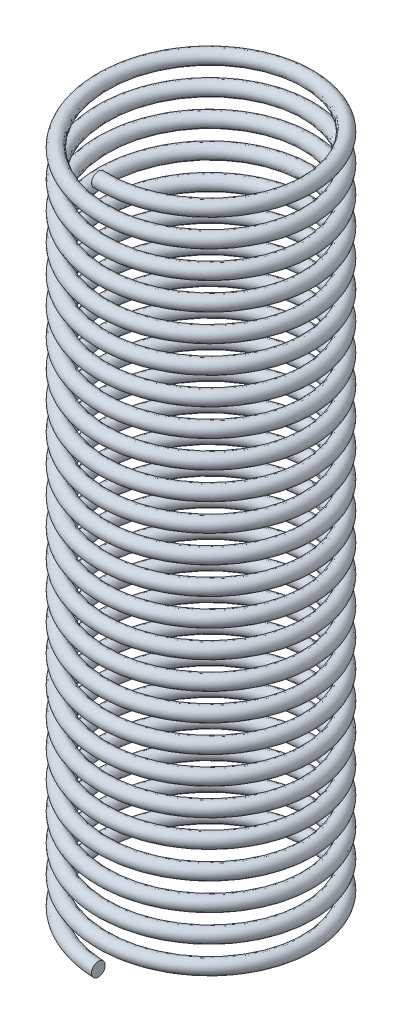
SolidWorks part; units mm, degrees
ref_plane "Front Plane" through (0, 0, 0) normal (0, 0, 1) x (1, 0, 0)
ref_plane "Top Plane" through (0, 0, 0) normal (0, 1, 0) x (1, 0, 0)
ref_plane "Right Plane" through (0, 0, 0) normal (1, 0, 0) x (0, 0, -1)
sketch "Sketch1" plane through (0, 0, 0) normal (0, 1, 0) x (1, 0, 0)
  circle A0 centre (0, 0) radius 75
  dimension "D1" = 150
curve "Helix/Spiral1" pitch 20 height 500 turns 25
sketch "Sketch2" plane through (0, 0, 0) normal (1, 0, 0) x (0, 0, -1)
  circle A0 centre (-75, 0) radius 5
  spline S0 degree 3 poles (-75, 0) (-75, 0.1732) (-74.3306, 0.5204) (-71.3449, 1.0406) (-66.4574, 1.5609) (-59.7983, 2.0812) (-51.545, 2.6015) (-41.9177, 3.1217) (-31.1729, 3.642) (-19.5972, 4.1623) (-7.499, 4.6826) (4.7991, 5.2029) (16.9693, 5.7232) (28.6871, 6.2435) (39.6401, 6.7638) (49.5365, 7.2841) (58.1123, 7.8044) (65.1389, 8.3247) (70.4291, 8.845) (73.8418, 9.3652) (75.286, 9.8855) (74.7233, 10.4058) (72.1686, 10.9261) (67.69, 11.4464) (61.4069, 11.9667) (53.4869, 12.487) (44.141, 13.0073) (33.6185, 13.5276) (22.1997, 14.0479) (10.1891, 14.5682) (-2.0931, 15.0884) (-14.3195, 15.6087) (-26.1641, 16.129) (-37.3113, 16.6493) (-47.4639, 17.1696) (-56.3511, 17.6899) (-63.7362, 18.2102) (-69.4222, 18.7305) (-73.2575, 19.2508) (-75.14, 19.7711) (-75.0193, 20.2914) (-72.8988, 20.8117) (-68.835, 21.3319) (-62.9362, 21.8522) (-55.3597, 22.3725) (-46.3073, 22.8928) (-36.0205, 23.4131) (-24.7735, 23.9334) (-12.8661, 24.4537) (-0.6157, 24.974) (11.6511, 25.4943) (23.6074, 26.0146) (34.9343, 26.5349) (45.3299, 27.0552) (54.5171, 27.5754) (62.2511, 28.0957) (68.3255, 28.616) (72.5785, 29.1363) (74.8968, 29.6566) (75.2184, 30.1769) (73.5349, 30.6972) (69.8911, 31.2175) (64.3841, 31.7378) (57.1608, 32.2581) (48.4137, 32.7784) (38.376, 33.2986) (27.3153, 33.8189) (15.5264, 34.3392) (3.3236, 34.8595) (-8.9677, 35.3798) (-21.0201, 35.9001) (-32.5121, 36.4204) (-43.1373, 36.9407) (-52.6127, 37.461) (-60.6854, 37.9813) (-67.1405, 38.5016) (-71.8057, 39.0219) (-74.5567, 39.5421) (-75.3202, 40.0624) (-74.0758, 40.5827) (-70.8568, 41.103) (-65.7488, 41.6233) (-58.8881, 42.1436) (-50.4575, 42.6639) (-40.6819, 43.1842) (-29.8218, 43.7045) (-18.1667, 44.2248) (-6.0273, 44.7451) (6.2728, 45.2653) (18.4056, 45.7856) (30.0478, 46.3059) (40.889, 46.8262) (50.6402, 47.3465) (59.0414, 47.8668) (65.8686, 48.3871) (70.94, 48.9074) (74.1203, 49.4277) (75.3246, 49.948) (74.521, 50.4683) (71.7308, 50.9886) (67.0284, 51.5088) (60.5392, 52.0291) (52.4361, 52.5494) (42.9352, 53.0697) (32.2897, 53.59) (20.7835, 54.1103) (8.7232, 54.6306) (-3.5697, 55.1509) (-15.7673, 55.6712) (-27.5447, 56.1915) (-38.5878, 56.7118) (-48.6022, 57.232) (-57.3209, 57.7523) (-64.5117, 58.2726) (-69.9826, 58.7929) (-73.588, 59.3132) (-75.2317, 59.8335) (-74.8698, 60.3538) (-72.5121, 60.8741) (-68.2214, 61.3944) (-62.112, 61.9147) (-54.3469, 62.435) (-45.133, 62.9553) (-34.7159, 63.4755) (-23.3734, 63.9958) (-11.4078, 64.5161) (0.8619, 65.0364) (13.1087, 65.5567) (25.006, 66.077) (36.2366, 66.5973) (46.5013, 67.1176) (55.5264, 67.6379) (63.0712, 68.1582) (68.9347, 68.6785) (72.9606, 69.1988) (75.0414, 69.719) (75.1219, 70.2393) (73.1997, 70.7596) (69.3262, 71.2799) (63.6046, 71.8002) (56.1874, 72.3205) (47.2724, 72.8408) (37.0972, 73.3611) (25.9331, 73.8814) (14.0776, 74.4017) (1.8469, 74.922) (-10.4331, 75.4422) (-22.4349, 75.9625) (-33.8387, 76.4828) (-44.3404, 77.0031) (-53.6601, 77.5234) (-61.5493, 78.0437) (-67.7977, 78.564) (-72.2388, 79.0843) (-74.7542, 79.6046) (-75.2768, 80.1249) (-73.7926, 80.6452) (-70.3413, 81.1655) (-65.0149, 81.6857) (-57.9552, 82.206) (-49.3507, 82.7263) (-39.4305, 83.2466) (-28.4592, 83.7669) (-16.7292, 84.2872) (-4.5533, 84.8075) (7.744, 85.3278) (19.8349, 85.8481) (31.397, 86.3684) (42.1221, 86.8887) (51.7243, 87.4089) (59.9477, 87.9292) (66.573, 88.4495) (71.4237, 88.9698) (74.3703, 89.4901) (75.3343, 90.0104) (74.2901, 90.5307) (71.2655, 91.051) (66.3411, 91.5713) (59.6482, 92.0916) (51.3651, 92.6119) (41.7128, 93.1322) (30.9486, 93.6524) (19.3593, 94.1727) (7.2539, 94.693) (-5.0449, 95.2133) (-17.2091, 95.7336) (-28.9146, 96.2539) (-39.8494, 96.7742) (-49.7218, 97.2945) (-58.2687, 97.8148) (-65.2623, 98.3351) (-70.5161, 98.8554) (-73.8902, 99.3757) (-75.2945, 99.8959) (-74.6916, 100.4162) (-72.0975, 100.9365) (-67.5815, 101.4568) (-61.2639, 101.9771) (-53.3132, 102.4974) (-43.9412, 103.0177) (-33.3979, 103.538) (-21.9642, 104.0583) (-9.9451, 104.5786) (2.3392, 105.0989) (14.5612, 105.6191) (26.3949, 106.1394) (37.5251, 106.6597) (47.6549, 107.18) (56.5143, 107.7003) (63.8671, 108.2206) (69.5174, 108.7409) (73.3146, 109.2612) (75.1573, 109.7815) (74.9964, 110.3018) (72.8363, 110.8221) (68.7346, 111.3424) (62.8005, 111.8626) (55.1923, 112.3829) (46.1128, 112.9032) (35.8041, 113.4235) (24.5408, 113.9438) (12.6234, 114.4641) (0.3694, 114.9844) (-11.8944, 115.5047) (-23.8411, 116.025) (-35.1523, 116.5453) (-45.5264, 117.0656) (-54.6868, 117.5858) (-62.3894, 118.1061) (-68.4289, 118.6264) (-72.6441, 119.1467) (-74.9229, 119.667) (-75.2043, 120.1873) (-73.481, 120.7076) (-69.7988, 121.2279) (-64.2559, 121.7482) (-57.0001, 122.2685) (-48.2248, 122.7888) (-38.1639, 123.3091) (-27.0857, 123.8293) (-15.2854, 124.3496) (-3.0776, 124.8699) (9.2122, 125.3902) (21.2565, 125.9105) (32.734, 126.4308) (43.339, 126.9511) (52.7886, 127.4714) (60.831, 127.9917) (67.2518, 128.512) (71.8798, 129.0323) (74.5916, 129.5525) (75.315, 130.0728) (74.0306, 130.5931) (70.7727, 131.1134) (65.6282, 131.6337) (58.7342, 132.154) (50.2744, 132.6743) (40.4744, 133.1946) (29.5955, 133.7149) (17.9276, 134.2352) (5.7818, 134.7555) (-6.5181, 135.2758) (-18.6443, 135.796) (-30.2735, 136.3163) (-41.0956, 136.8366) (-50.8222, 137.3569) (-59.194, 137.8772) (-65.9878, 138.3975) (-71.0225, 138.9178) (-74.1639, 139.4381) (-75.3283, 139.9584) (-74.4845, 140.4787) (-71.6552, 140.999) (-66.9156, 141.5193) (-60.3923, 142.0395) (-52.259, 142.5598) (-42.7326, 143.0801) (-32.067, 143.6004) (-20.5466, 144.1207) (-8.4785, 144.641) (3.8156, 145.1613) (16.0081, 145.6816) (27.7738, 146.2019) (38.7991, 146.7222) (48.7901, 147.2425) (57.4804, 147.7627) (64.6385, 148.283) (70.0734, 148.8033) (73.6403, 149.3236) (75.2442, 149.8439) (74.8421, 150.3642) (72.445, 150.8845) (68.1166, 151.4048) (61.9723, 151.9251) (54.176, 152.4454) (44.9355, 152.9657) (34.4971, 153.486) (23.1391, 154.0062) (11.1643, 154.5265) (-1.1082, 155.0468) (-13.3511, 155.5671) (-25.2381, 156.0874) (-36.4524, 156.6077) (-46.6948, 157.128) (-55.6925, 157.6483) (-63.2056, 158.1686) (-69.0337, 158.6889) (-73.0215, 159.2092) (-75.0628, 159.7294) (-75.103, 160.2497) (-73.1411, 160.77) (-69.2294, 161.2903) (-63.4722, 161.8106) (-56.023, 162.3309) (-47.0804, 162.8512) (-36.8826, 163.3715) (-25.7017, 163.8918) (-13.8356, 164.4121) (-1.6007, 164.9324) (10.6769, 165.4527) (22.6699, 165.9729) (34.0585, 166.4932) (44.5392, 167.0135) (53.8326, 167.5338) (61.691, 168.0541) (67.9047, 168.5744) (72.3083, 169.0947) (74.7843, 169.615) (75.2667, 170.1353) (73.7426, 170.6556) (70.2528, 171.1759) (64.8901, 171.6961) (57.7976, 172.2164) (49.1643, 172.7367) (39.2204, 173.257) (28.231, 173.7773) (16.489, 174.2976) (4.3075, 174.8179) (-7.9889, 175.3382) (-20.0723, 175.8585) (-31.6207, 176.3788) (-42.3261, 176.8991) (-51.9031, 177.4194) (-60.0966, 177.9396) (-66.688, 178.4599) (-71.5016, 178.9802) (-74.4091, 179.5005) (-75.3331, 180.0208) (-74.2488, 180.5411) (-71.1853, 181.0614) (-66.224, 181.5817) (-59.4974, 182.102) (-51.1847, 182.6223) (-41.5075, 183.1426) (-30.7239, 183.6629) (-19.1211, 184.1831) (-7.0087, 184.7034) (5.2906, 185.2237) (17.4488, 185.744) (29.1419, 186.2643) (40.0581, 186.7846) (49.9065, 187.3049) (58.4245, 187.8252) (65.385, 188.3455) (70.6024, 188.8658) (73.9378, 189.3861) (75.3021, 189.9063) (74.659, 190.4266) (72.0257, 190.9469) (67.4723, 191.4672) (61.1203, 191.9875) (53.1389, 192.5078) (43.741, 193.0281) (33.177, 193.5484) (21.7285, 194.0687) (9.7009, 194.589) (-2.5854, 195.1093) (-14.8027, 195.6296) (-26.6255, 196.1498) (-37.7384, 196.6701) (-47.8454, 197.1904) (-56.6768, 197.7107) (-63.9974, 198.231) (-69.612, 198.7513) (-73.3708, 199.2716) (-75.1737, 199.7919) (-74.9727, 200.3122) (-72.7731, 200.8325) (-68.6334, 201.3528) (-62.6642, 201.873) (-55.0244, 202.3933) (-45.9178, 202.9136) (-35.5872, 203.4339) (-24.3078, 203.9542) (-12.3805, 204.4745) (-0.1231, 204.9948) (12.1375, 205.5151) (24.0746, 206.0354) (35.3699, 206.5557) (45.7223, 207.076) (54.8559, 207.5963) (62.5271, 208.1165) (68.5315, 208.6368) (72.709, 209.1571) (74.9482, 209.6774) (75.1894, 210.1977) (73.4263, 210.718) (69.7058, 211.2383) (64.127, 211.7586) (56.8388, 212.2789) (48.0353, 212.7992) (37.9514, 213.3195) (26.8557, 213.8398) (15.0441, 214.36) (2.8315, 214.8803) (-9.4566, 215.4006) (-21.4926, 215.9209) (-32.9557, 216.4412) (-43.5402, 216.9615) (-52.9641, 217.4818) (-60.976, 218.0021) (-67.3624, 218.5224) (-71.9531, 219.0427) (-74.6257, 219.563) (-75.3089, 220.0832) (-73.9846, 220.6035) (-70.688, 221.1238) (-65.5069, 221.6441) (-58.5796, 222.1644) (-50.0907, 222.6847) (-40.2665, 223.205) (-29.3689, 223.7253) (-17.6883, 224.2456) (-5.5362, 224.7659) (6.7635, 225.2862) (18.8828, 225.8065) (30.4988, 226.3267) (41.3018, 226.847) (51.0037, 227.3673) (59.346, 227.8876) (66.1063, 228.4079) (71.1043, 228.9282) (74.2068, 229.4485) (75.3311, 229.9688) (74.4472, 230.4891) (71.5788, 231.0094) (66.8022, 231.5297) (60.2448, 232.0499) (52.0813, 232.5702) (42.5296, 233.0905) (31.844, 233.6108) (20.3096, 234.1311) (8.2338, 234.6514) (-4.0616, 235.1717) (-16.2486, 235.692) (-28.0025, 236.2123) (-39.01, 236.7326) (-48.9775, 237.2529) (-57.6393, 237.7732) (-64.7646, 238.2934) (-70.1635, 238.8137) (-73.6919, 239.334) (-75.2558, 239.8543) (-74.8136, 240.3746) (-72.377, 240.8949) (-68.011, 241.4152) (-61.832, 241.9355) (-54.0046, 242.4558) (-44.7376, 242.9761) (-34.278, 243.4964) (-22.9046, 244.0166) (-10.9207, 244.5369) (1.3544, 245.0572) (13.5934, 245.5775) (25.4701, 246.0978) (36.6677, 246.6181) (46.8879, 247.1384) (55.8581, 247.6587) (63.3393, 248.179) (69.1319, 248.6993) (73.0817, 249.2196) (75.0833, 249.7399) (75.0833, 250.2601) (73.0817, 250.7804) (69.1319, 251.3007) (63.3393, 251.821) (55.8581, 252.3413) (46.8879, 252.8616) (36.6677, 253.3819) (25.4701, 253.9022) (13.5934, 254.4225) (1.3544, 254.9428) (-10.9207, 255.4631) (-22.9046, 255.9834) (-34.278, 256.5036) (-44.7376, 257.0239) (-54.0046, 257.5442) (-61.832, 258.0645) (-68.011, 258.5848) (-72.377, 259.1051) (-74.8136, 259.6254) (-75.2558, 260.1457) (-73.6919, 260.666) (-70.1635, 261.1863) (-64.7646, 261.7066) (-57.6393, 262.2268) (-48.9775, 262.7471) (-39.01, 263.2674) (-28.0025, 263.7877) (-16.2486, 264.308) (-4.0616, 264.8283) (8.2338, 265.3486) (20.3096, 265.8689) (31.844, 266.3892) (42.5296, 266.9095) (52.0813, 267.4298) (60.2448, 267.9501) (66.8022, 268.4703) (71.5788, 268.9906) (74.4472, 269.5109) (75.3311, 270.0312) (74.2068, 270.5515) (71.1043, 271.0718) (66.1063, 271.5921) (59.346, 272.1124) (51.0037, 272.6327) (41.3018, 273.153) (30.4988, 273.6733) (18.8828, 274.1935) (6.7635, 274.7138) (-5.5362, 275.2341) (-17.6883, 275.7544) (-29.3689, 276.2747) (-40.2665, 276.795) (-50.0907, 277.3153) (-58.5796, 277.8356) (-65.5069, 278.3559) (-70.688, 278.8762) (-73.9846, 279.3965) (-75.3089, 279.9168) (-74.6257, 280.437) (-71.9531, 280.9573) (-67.3624, 281.4776) (-60.976, 281.9979) (-52.9641, 282.5182) (-43.5402, 283.0385) (-32.9557, 283.5588) (-21.4926, 284.0791) (-9.4566, 284.5994) (2.8315, 285.1197) (15.0441, 285.64) (26.8557, 286.1602) (37.9514, 286.6805) (48.0353, 287.2008) (56.8388, 287.7211) (64.127, 288.2414) (69.7058, 288.7617) (73.4263, 289.282) (75.1894, 289.8023) (74.9482, 290.3226) (72.709, 290.8429) (68.5315, 291.3632) (62.5271, 291.8835) (54.8559, 292.4037) (45.7223, 292.924) (35.3699, 293.4443) (24.0746, 293.9646) (12.1375, 294.4849) (-0.1231, 295.0052) (-12.3805, 295.5255) (-24.3078, 296.0458) (-35.5872, 296.5661) (-45.9178, 297.0864) (-55.0244, 297.6067) (-62.6642, 298.127) (-68.6334, 298.6472) (-72.7731, 299.1675) (-74.9727, 299.6878) (-75.1737, 300.2081) (-73.3708, 300.7284) (-69.612, 301.2487) (-63.9974, 301.769) (-56.6768, 302.2893) (-47.8454, 302.8096) (-37.7384, 303.3299) (-26.6255, 303.8502) (-14.8027, 304.3704) (-2.5854, 304.8907) (9.7009, 305.411) (21.7285, 305.9313) (33.177, 306.4516) (43.741, 306.9719) (53.1389, 307.4922) (61.1203, 308.0125) (67.4723, 308.5328) (72.0257, 309.0531) (74.659, 309.5734) (75.3021, 310.0937) (73.9378, 310.6139) (70.6024, 311.1342) (65.385, 311.6545) (58.4245, 312.1748) (49.9065, 312.6951) (40.0581, 313.2154) (29.1419, 313.7357) (17.4488, 314.256) (5.2906, 314.7763) (-7.0087, 315.2966) (-19.1211, 315.8169) (-30.7239, 316.3371) (-41.5075, 316.8574) (-51.1847, 317.3777) (-59.4974, 317.898) (-66.224, 318.4183) (-71.1853, 318.9386) (-74.2488, 319.4589) (-75.3331, 319.9792) (-74.4091, 320.4995) (-71.5016, 321.0198) (-66.688, 321.5401) (-60.0966, 322.0604) (-51.9031, 322.5806) (-42.3261, 323.1009) (-31.6207, 323.6212) (-20.0723, 324.1415) (-7.9889, 324.6618) (4.3075, 325.1821) (16.489, 325.7024) (28.231, 326.2227) (39.2204, 326.743) (49.1643, 327.2633) (57.7976, 327.7836) (64.8901, 328.3039) (70.2528, 328.8241) (73.7426, 329.3444) (75.2667, 329.8647) (74.7843, 330.385) (72.3083, 330.9053) (67.9047, 331.4256) (61.691, 331.9459) (53.8326, 332.4662) (44.5392, 332.9865) (34.0585, 333.5068) (22.6699, 334.0271) (10.6769, 334.5473) (-1.6007, 335.0676) (-13.8356, 335.5879) (-25.7017, 336.1082) (-36.8826, 336.6285) (-47.0804, 337.1488) (-56.023, 337.6691) (-63.4722, 338.1894) (-69.2294, 338.7097) (-73.1411, 339.23) (-75.103, 339.7503) (-75.0628, 340.2706) (-73.0215, 340.7908) (-69.0337, 341.3111) (-63.2056, 341.8314) (-55.6925, 342.3517) (-46.6948, 342.872) (-36.4524, 343.3923) (-25.2381, 343.9126) (-13.3511, 344.4329) (-1.1082, 344.9532) (11.1643, 345.4735) (23.1391, 345.9938) (34.4971, 346.514) (44.9355, 347.0343) (54.176, 347.5546) (61.9723, 348.0749) (68.1166, 348.5952) (72.445, 349.1155) (74.8421, 349.6358) (75.2442, 350.1561) (73.6403, 350.6764) (70.0734, 351.1967) (64.6385, 351.717) (57.4804, 352.2373) (48.7901, 352.7575) (38.7991, 353.2778) (27.7738, 353.7981) (16.0081, 354.3184) (3.8156, 354.8387) (-8.4785, 355.359) (-20.5466, 355.8793) (-32.067, 356.3996) (-42.7326, 356.9199) (-52.259, 357.4402) (-60.3923, 357.9605) (-66.9156, 358.4807) (-71.6552, 359.001) (-74.4845, 359.5213) (-75.3283, 360.0416) (-74.1639, 360.5619) (-71.0225, 361.0822) (-65.9878, 361.6025) (-59.194, 362.1228) (-50.8222, 362.6431) (-41.0956, 363.1634) (-30.2735, 363.6837) (-18.6443, 364.204) (-6.5181, 364.7242) (5.7818, 365.2445) (17.9276, 365.7648) (29.5955, 366.2851) (40.4744, 366.8054) (50.2744, 367.3257) (58.7342, 367.846) (65.6282, 368.3663) (70.7727, 368.8866) (74.0306, 369.4069) (75.315, 369.9272) (74.5916, 370.4475) (71.8798, 370.9677) (67.2518, 371.488) (60.831, 372.0083) (52.7886, 372.5286) (43.339, 373.0489) (32.734, 373.5692) (21.2565, 374.0895) (9.2122, 374.6098) (-3.0776, 375.1301) (-15.2854, 375.6504) (-27.0857, 376.1707) (-38.1639, 376.6909) (-48.2248, 377.2112) (-57.0001, 377.7315) (-64.2559, 378.2518) (-69.7988, 378.7721) (-73.481, 379.2924) (-75.2043, 379.8127) (-74.9229, 380.333) (-72.6441, 380.8533) (-68.4289, 381.3736) (-62.3894, 381.8939) (-54.6868, 382.4142) (-45.5264, 382.9344) (-35.1523, 383.4547) (-23.8411, 383.975) (-11.8944, 384.4953) (0.3694, 385.0156) (12.6234, 385.5359) (24.5408, 386.0562) (35.8041, 386.5765) (46.1128, 387.0968) (55.1923, 387.6171) (62.8005, 388.1374) (68.7346, 388.6576) (72.8363, 389.1779) (74.9964, 389.6982) (75.1573, 390.2185) (73.3146, 390.7388) (69.5174, 391.2591) (63.8671, 391.7794) (56.5143, 392.2997) (47.6549, 392.82) (37.5251, 393.3403) (26.3949, 393.8606) (14.5612, 394.3809) (2.3392, 394.9011) (-9.9451, 395.4214) (-21.9642, 395.9417) (-33.3979, 396.462) (-43.9412, 396.9823) (-53.3132, 397.5026) (-61.2639, 398.0229) (-67.5815, 398.5432) (-72.0975, 399.0635) (-74.6916, 399.5838) (-75.2945, 400.1041) (-73.8902, 400.6243) (-70.5161, 401.1446) (-65.2623, 401.6649) (-58.2687, 402.1852) (-49.7218, 402.7055) (-39.8494, 403.2258) (-28.9146, 403.7461) (-17.2091, 404.2664) (-5.0449, 404.7867) (7.2539, 405.307) (19.3593, 405.8273) (30.9486, 406.3476) (41.7128, 406.8678) (51.3651, 407.3881) (59.6482, 407.9084) (66.3411, 408.4287) (71.2655, 408.949) (74.2901, 409.4693) (75.3343, 409.9896) (74.3703, 410.5099) (71.4237, 411.0302) (66.573, 411.5505) (59.9477, 412.0708) (51.7243, 412.5911) (42.1221, 413.1113) (31.397, 413.6316) (19.8349, 414.1519) (7.744, 414.6722) (-4.5533, 415.1925) (-16.7292, 415.7128) (-28.4592, 416.2331) (-39.4305, 416.7534) (-49.3507, 417.2737) (-57.9552, 417.794) (-65.0149, 418.3143) (-70.3413, 418.8345) (-73.7926, 419.3548) (-75.2768, 419.8751) (-74.7542, 420.3954) (-72.2388, 420.9157) (-67.7977, 421.436) (-61.5493, 421.9563) (-53.6601, 422.4766) (-44.3404, 422.9969) (-33.8387, 423.5172) (-22.4349, 424.0375) (-10.4331, 424.5578) (1.8469, 425.078) (14.0776, 425.5983) (25.9331, 426.1186) (37.0972, 426.6389) (47.2724, 427.1592) (56.1874, 427.6795) (63.6046, 428.1998) (69.3262, 428.7201) (73.1997, 429.2404) (75.1219, 429.7607) (75.0414, 430.281) (72.9606, 430.8012) (68.9347, 431.3215) (63.0712, 431.8418) (55.5264, 432.3621) (46.5013, 432.8824) (36.2366, 433.4027) (25.006, 433.923) (13.1087, 434.4433) (0.8619, 434.9636) (-11.4078, 435.4839) (-23.3734, 436.0042) (-34.7159, 436.5245) (-45.133, 437.0447) (-54.3469, 437.565) (-62.112, 438.0853) (-68.2214, 438.6056) (-72.5121, 439.1259) (-74.8698, 439.6462) (-75.2317, 440.1665) (-73.588, 440.6868) (-69.9826, 441.2071) (-64.5117, 441.7274) (-57.3209, 442.2477) (-48.6022, 442.768) (-38.5878, 443.2882) (-27.5447, 443.8085) (-15.7673, 444.3288) (-3.5697, 444.8491) (8.7232, 445.3694) (20.7835, 445.8897) (32.2897, 446.41) (42.9352, 446.9303) (52.4361, 447.4506) (60.5392, 447.9709) (67.0284, 448.4912) (71.7308, 449.0114) (74.521, 449.5317) (75.3246, 450.052) (74.1203, 450.5723) (70.94, 451.0926) (65.8686, 451.6129) (59.0414, 452.1332) (50.6402, 452.6535) (40.889, 453.1738) (30.0478, 453.6941) (18.4056, 454.2144) (6.2728, 454.7347) (-6.0273, 455.2549) (-18.1667, 455.7752) (-29.8218, 456.2955) (-40.6819, 456.8158) (-50.4575, 457.3361) (-58.8881, 457.8564) (-65.7488, 458.3767) (-70.8568, 458.897) (-74.0758, 459.4173) (-75.3202, 459.9376) (-74.5567, 460.4579) (-71.8057, 460.9781) (-67.1405, 461.4984) (-60.6854, 462.0187) (-52.6127, 462.539) (-43.1373, 463.0593) (-32.5121, 463.5796) (-21.0201, 464.0999) (-8.9677, 464.6202) (3.3236, 465.1405) (15.5264, 465.6608) (27.3153, 466.1811) (38.376, 466.7014) (48.4137, 467.2216) (57.1608, 467.7419) (64.3841, 468.2622) (69.8911, 468.7825) (73.5349, 469.3028) (75.2184, 469.8231) (74.8968, 470.3434) (72.5785, 470.8637) (68.3255, 471.384) (62.2511, 471.9043) (54.5171, 472.4246) (45.3299, 472.9448) (34.9343, 473.4651) (23.6074, 473.9854) (11.6511, 474.5057) (-0.6157, 475.026) (-12.8661, 475.5463) (-24.7735, 476.0666) (-36.0205, 476.5869) (-46.3073, 477.1072) (-55.3597, 477.6275) (-62.9362, 478.1478) (-68.835, 478.6681) (-72.8988, 479.1883) (-75.0193, 479.7086) (-75.14, 480.2289) (-73.2575, 480.7492) (-69.4222, 481.2695) (-63.7362, 481.7898) (-56.3511, 482.3101) (-47.4639, 482.8304) (-37.3113, 483.3507) (-26.1641, 483.871) (-14.3195, 484.3913) (-2.0931, 484.9116) (10.1891, 485.4318) (22.1997, 485.9521) (33.6185, 486.4724) (44.141, 486.9927) (53.4869, 487.513) (61.4069, 488.0333) (67.69, 488.5536) (72.1686, 489.0739) (74.7233, 489.5942) (75.286, 490.1145) (73.8418, 490.6348) (70.4291, 491.155) (65.1389, 491.6753) (58.1123, 492.1956) (49.5365, 492.7159) (39.6401, 493.2362) (28.6871, 493.7565) (16.9693, 494.2768) (4.7991, 494.7971) (-7.499, 495.3174) (-19.5972, 495.8377) (-31.1729, 496.358) (-41.9177, 496.8783) (-51.545, 497.3985) (-59.7983, 497.9188) (-66.4574, 498.4391) (-71.3449, 498.9594) (-74.3306, 499.4796) (-75, 499.8268) (-75, 500) knots 0 0 0 0 0.001041 0.002081 0.003122 0.004162 0.005203 0.006243 0.007284 0.008325 0.009365 0.010406 0.011446 0.012487 0.013528 0.014568 0.015609 0.016649 0.01769 0.01873 0.019771 0.020812 0.021852 0.022893 0.023933 0.024974 0.026015 0.027055 0.028096 0.029136 0.030177 0.031217 0.032258 0.033299 0.034339 0.03538 0.03642 0.037461 0.038502 0.039542 0.040583 0.041623 0.042664 0.043704 0.044745 0.045786 0.046826 0.047867 0.048907 0.049948 0.050989 0.052029 0.05307 0.05411 0.055151 0.056191 0.057232 0.058273 0.059313 0.060354 0.061394 0.062435 0.063476 0.064516 0.065557 0.066597 0.067638 0.068678 0.069719 0.07076 0.0718 0.072841 0.073881 0.074922 0.075963 0.077003 0.078044 0.079084 0.080125 0.081165 0.082206 0.083247 0.084287 0.085328 0.086368 0.087409 0.08845 0.08949 0.090531 0.091571 0.092612 0.093652 0.094693 0.095734 0.096774 0.097815 0.098855 0.099896 0.100937 0.101977 0.103018 0.104058 0.105099 0.106139 0.10718 0.108221 0.109261 0.110302 0.111342 0.112383 0.113424 0.114464 0.115505 0.116545 0.117586 0.118626 0.119667 0.120708 0.121748 0.122789 0.123829 0.12487 0.125911 0.126951 0.127992 0.129032 0.130073 0.131113 0.132154 0.133195 0.134235 0.135276 0.136316 0.137357 0.138398 0.139438 0.140479 0.141519 0.14256 0.1436 0.144641 0.145682 0.146722 0.147763 0.148803 0.149844 0.150884 0.151925 0.152966 0.154006 0.155047 0.156087 0.157128 0.158169 0.159209 0.16025 0.16129 0.162331 0.163371 0.164412 0.165453 0.166493 0.167534 0.168574 0.169615 0.170656 0.171696 0.172737 0.173777 0.174818 0.175858 0.176899 0.17794 0.17898 0.180021 0.181061 0.182102 0.183143 0.184183 0.185224 0.186264 0.187305 0.188345 0.189386 0.190427 0.191467 0.192508 0.193548 0.194589 0.19563 0.19667 0.197711 0.198751 0.199792 0.200832 0.201873 0.202914 0.203954 0.204995 0.206035 0.207076 0.208117 0.209157 0.210198 0.211238 0.212279 0.213319 0.21436 0.215401 0.216441 0.217482 0.218522 0.219563 0.220604 0.221644 0.222685 0.223725 0.224766 0.225806 0.226847 0.227888 0.228928 0.229969 0.231009 0.23205 0.233091 0.234131 0.235172 0.236212 0.237253 0.238293 0.239334 0.240375 0.241415 0.242456 0.243496 0.244537 0.245578 0.246618 0.247659 0.248699 0.24974 0.25078 0.251821 0.252862 0.253902 0.254943 0.255983 0.257024 0.258065 0.259105 0.260146 0.261186 0.262227 0.263267 0.264308 0.265349 0.266389 0.26743 0.26847 0.269511 0.270552 0.271592 0.272633 0.273673 0.274714 0.275754 0.276795 0.277836 0.278876 0.279917 0.280957 0.281998 0.283039 0.284079 0.28512 0.28616 0.287201 0.288241 0.289282 0.290323 0.291363 0.292404 0.293444 0.294485 0.295525 0.296566 0.297607 0.298647 0.299688 0.300728 0.301769 0.30281 0.30385 0.304891 0.305931 0.306972 0.308012 0.309053 0.310094 0.311134 0.312175 0.313215 0.314256 0.315297 0.316337 0.317378 0.318418 0.319459 0.320499 0.32154 0.322581 0.323621 0.324662 0.325702 0.326743 0.327784 0.328824 0.329865 0.330905 0.331946 0.332986 0.334027 0.335068 0.336108 0.337149 0.338189 0.33923 0.340271 0.341311 0.342352 0.343392 0.344433 0.345473 0.346514 0.347555 0.348595 0.349636 0.350676 0.351717 0.352758 0.353798 0.354839 0.355879 0.35692 0.35796 0.359001 0.360042 0.361082 0.362123 0.363163 0.364204 0.365245 0.366285 0.367326 0.368366 0.369407 0.370447 0.371488 0.372529 0.373569 0.37461 0.37565 0.376691 0.377732 0.378772 0.379813 0.380853 0.381894 0.382934 0.383975 0.385016 0.386056 0.387097 0.388137 0.389178 0.390219 0.391259 0.3923 0.39334 0.394381 0.395421 0.396462 0.397503 0.398543 0.399584 0.400624 0.401665 0.402706 0.403746 0.404787 0.405827 0.406868 0.407908 0.408949 0.40999 0.41103 0.412071 0.413111 0.414152 0.415193 0.416233 0.417274 0.418314 0.419355 0.420395 0.421436 0.422477 0.423517 0.424558 0.425598 0.426639 0.42768 0.42872 0.429761 0.430801 0.431842 0.432882 0.433923 0.434964 0.436004 0.437045 0.438085 0.439126 0.440166 0.441207 0.442248 0.443288 0.444329 0.445369 0.44641 0.447451 0.448491 0.449532 0.450572 0.451613 0.452653 0.453694 0.454735 0.455775 0.456816 0.457856 0.458897 0.459938 0.460978 0.462019 0.463059 0.4641 0.46514 0.466181 0.467222 0.468262 0.469303 0.470343 0.471384 0.472425 0.473465 0.474506 0.475546 0.476587 0.477627 0.478668 0.479709 0.480749 0.48179 0.48283 0.483871 0.484912 0.485952 0.486993 0.488033 0.489074 0.490114 0.491155 0.492196 0.493236 0.494277 0.495317 0.496358 0.497399 0.498439 0.49948 0.50052 0.501561 0.502601 0.503642 0.504683 0.505723 0.506764 0.507804 0.508845 0.509886 0.510926 0.511967 0.513007 0.514048 0.515088 0.516129 0.51717 0.51821 0.519251 0.520291 0.521332 0.522373 0.523413 0.524454 0.525494 0.526535 0.527575 0.528616 0.529657 0.530697 0.531738 0.532778 0.533819 0.53486 0.5359 0.536941 0.537981 0.539022 0.540062 0.541103 0.542144 0.543184 0.544225 0.545265 0.546306 0.547347 0.548387 0.549428 0.550468 0.551509 0.552549 0.55359 0.554631 0.555671 0.556712 0.557752 0.558793 0.559834 0.560874 0.561915 0.562955 0.563996 0.565036 0.566077 0.567118 0.568158 0.569199 0.570239 0.57128 0.57232 0.573361 0.574402 0.575442 0.576483 0.577523 0.578564 0.579605 0.580645 0.581686 0.582726 0.583767 0.584807 0.585848 0.586889 0.587929 0.58897 0.59001 0.591051 0.592092 0.593132 0.594173 0.595213 0.596254 0.597294 0.598335 0.599376 0.600416 0.601457 0.602497 0.603538 0.604579 0.605619 0.60666 0.6077 0.608741 0.609781 0.610822 0.611863 0.612903 0.613944 0.614984 0.616025 0.617066 0.618106 0.619147 0.620187 0.621228 0.622268 0.623309 0.62435 0.62539 0.626431 0.627471 0.628512 0.629553 0.630593 0.631634 0.632674 0.633715 0.634755 0.635796 0.636837 0.637877 0.638918 0.639958 0.640999 0.64204 0.64308 0.644121 0.645161 0.646202 0.647242 0.648283 0.649324 0.650364 0.651405 0.652445 0.653486 0.654527 0.655567 0.656608 0.657648 0.658689 0.659729 0.66077 0.661811 0.662851 0.663892 0.664932 0.665973 0.667014 0.668054 0.669095 0.670135 0.671176 0.672216 0.673257 0.674298 0.675338 0.676379 0.677419 0.67846 0.679501 0.680541 0.681582 0.682622 0.683663 0.684703 0.685744 0.686785 0.687825 0.688866 0.689906 0.690947 0.691988 0.693028 0.694069 0.695109 0.69615 0.69719 0.698231 0.699272 0.700312 0.701353 0.702393 0.703434 0.704475 0.705515 0.706556 0.707596 0.708637 0.709677 0.710718 0.711759 0.712799 0.71384 0.71488 0.715921 0.716961 0.718002 0.719043 0.720083 0.721124 0.722164 0.723205 0.724246 0.725286 0.726327 0.727367 0.728408 0.729448 0.730489 0.73153 0.73257 0.733611 0.734651 0.735692 0.736733 0.737773 0.738814 0.739854 0.740895 0.741935 0.742976 0.744017 0.745057 0.746098 0.747138 0.748179 0.74922 0.75026 0.751301 0.752341 0.753382 0.754422 0.755463 0.756504 0.757544 0.758585 0.759625 0.760666 0.761707 0.762747 0.763788 0.764828 0.765869 0.766909 0.76795 0.768991 0.770031 0.771072 0.772112 0.773153 0.774194 0.775234 0.776275 0.777315 0.778356 0.779396 0.780437 0.781478 0.782518 0.783559 0.784599 0.78564 0.786681 0.787721 0.788762 0.789802 0.790843 0.791883 0.792924 0.793965 0.795005 0.796046 0.797086 0.798127 0.799168 0.800208 0.801249 0.802289 0.80333 0.80437 0.805411 0.806452 0.807492 0.808533 0.809573 0.810614 0.811655 0.812695 0.813736 0.814776 0.815817 0.816857 0.817898 0.818939 0.819979 0.82102 0.82206 0.823101 0.824142 0.825182 0.826223 0.827263 0.828304 0.829344 0.830385 0.831426 0.832466 0.833507 0.834547 0.835588 0.836629 0.837669 0.83871 0.83975 0.840791 0.841831 0.842872 0.843913 0.844953 0.845994 0.847034 0.848075 0.849116 0.850156 0.851197 0.852237 0.853278 0.854318 0.855359 0.8564 0.85744 0.858481 0.859521 0.860562 0.861602 0.862643 0.863684 0.864724 0.865765 0.866805 0.867846 0.868887 0.869927 0.870968 0.872008 0.873049 0.874089 0.87513 0.876171 0.877211 0.878252 0.879292 0.880333 0.881374 0.882414 0.883455 0.884495 0.885536 0.886576 0.887617 0.888658 0.889698 0.890739 0.891779 0.89282 0.893861 0.894901 0.895942 0.896982 0.898023 0.899063 0.900104 0.901145 0.902185 0.903226 0.904266 0.905307 0.906348 0.907388 0.908429 0.909469 0.91051 0.91155 0.912591 0.913632 0.914672 0.915713 0.916753 0.917794 0.918835 0.919875 0.920916 0.921956 0.922997 0.924037 0.925078 0.926119 0.927159 0.9282 0.92924 0.930281 0.931322 0.932362 0.933403 0.934443 0.935484 0.936524 0.937565 0.938606 0.939646 0.940687 0.941727 0.942768 0.943809 0.944849 0.94589 0.94693 0.947971 0.949011 0.950052 0.951093 0.952133 0.953174 0.954214 0.955255 0.956296 0.957336 0.958377 0.959417 0.960458 0.961498 0.962539 0.96358 0.96462 0.965661 0.966701 0.967742 0.968783 0.969823 0.970864 0.971904 0.972945 0.973985 0.975026 0.976067 0.977107 0.978148 0.979188 0.980229 0.98127 0.98231 0.983351 0.984391 0.985432 0.986472 0.987513 0.988554 0.989594 0.990635 0.991675 0.992716 0.993757 0.994797 0.995838 0.996878 0.997919 0.998959 1 1 1 1 construction
  dimension "D1" = 10
sweep "Sweep1" add profiles "Sketch2" path "Helix/Spiral1"
